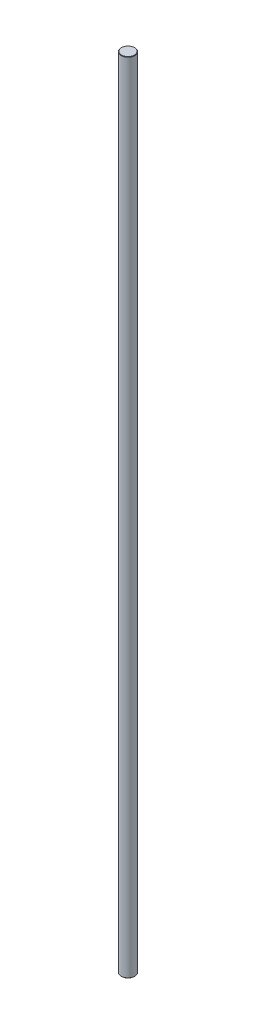
SolidWorks part; units mm, degrees
ref_plane "Front Plane" through (0, 0, 0) normal (0, 0, 1) x (1, 0, 0)
ref_plane "Top Plane" through (0, 0, 0) normal (0, 1, 0) x (1, 0, 0)
ref_plane "Right Plane" through (0, 0, 0) normal (1, 0, 0) x (0, 0, -1)
sketch "Sketch1" plane through (0, 0, 0) normal (0, 1, 0) x (1, 0, 0)
  circle A0 centre (0, 0) radius 4
  dimension "D1" = 8
extrude "Boss-Extrude1" add sketch "Sketch1" along normal mid plane 470
cosmetic thread "Cosmetic Thread1" parameters "D2"=6.619
chamfer "Chamfer1" distance 0.2 angle 45 2 edges at (0, -235, 4) (0, 235, 4)
